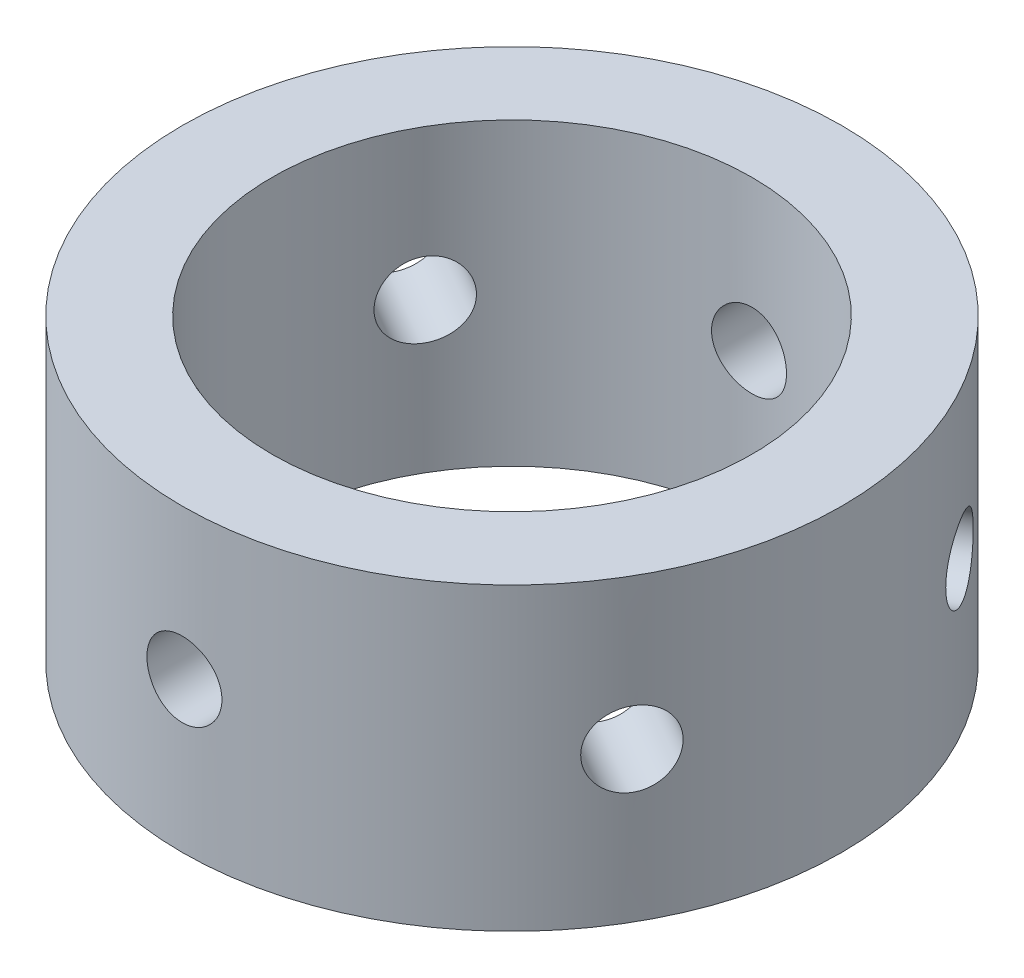
SolidWorks part; units mm, degrees
material "6061-T6 (SS)"
ref_plane "Front Plane" through (0, 0, 0) normal (0, 0, 1) x (1, 0, 0)
ref_plane "Top Plane" through (0, 0, 0) normal (0, 1, 0) x (1, 0, 0)
ref_plane "Right Plane" through (0, 0, 0) normal (1, 0, 0) x (0, 0, -1)
sketch "Sketch1" plane through (0, 0, 0) normal (0, 1, 0) x (1, 0, 0)
  circle A0 centre (0, 0) radius 34.8996
  circle A4 centre (0, 0) radius 25.4
  dimension "D1" = 69.7992
  dimension "D2" = 50.8
extrude "Boss-Extrude1" add sketch "Sketch1" along normal blind 31.75 contours A0
ref_plane "Plane2" through (0, 0, 34.8996) normal (0, 0, 1) x (1, 0, 0)
hole_wizard "Tap Drill for 3/8-16 Tap1" positions "Sketch21" profile "Sketch22" hole size "3/8-16" standard "ANSI Inch"
sketch "Sketch21" plane through (0, 0, 34.8996) normal (0, 0, 1) x (1, 0, 0)
  line L1 (0, 31.75) -> (0, 0) construction
  line L2 (34.8996, 31.75) -> (-34.8996, 31.75) construction
  point P15 (0, 15.875)
sketch "Sketch22" plane through (0, 15.875, 34.8996) normal (1, 0, 0) x (0, -1, 0)
  line L0 (0, 0) -> (0, 9.4996)
  line L1 (0, 9.4996) -> (3.9687, 9.4996)
  line L2 (3.9687, 9.4996) -> (3.9687, 0)
  line L5 (3.9687, 0) -> (0, 0)
  line L11 (0, -6.35) -> (0, 107.95) construction
  dimension "Thru Hole Dia." = 7.9375
  dimension "Thru Hole Depth" = 9.4996
pattern_circular "CirPattern2" count 6 over 360 about axis through (0, 31.75, 0) along (0, -1, 0) of "Tap Drill for 3/8-16 Tap1"
